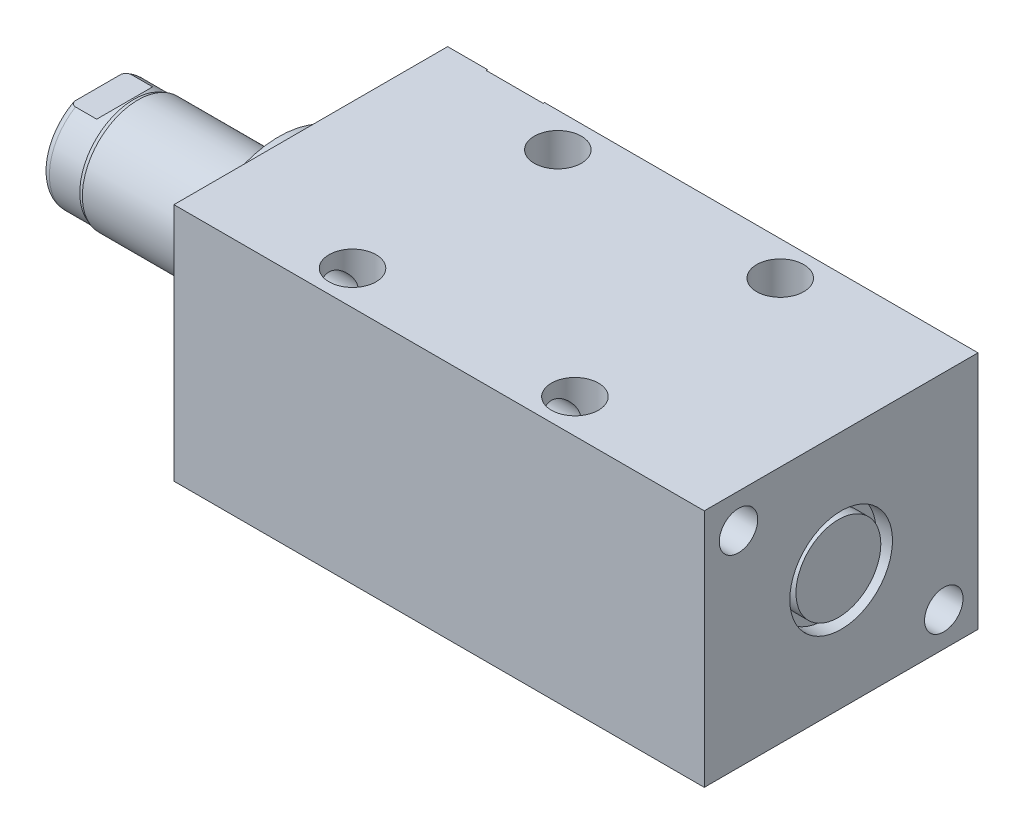
SolidWorks part; units mm, degrees
material "Alloy Steel"
ref_plane "Front Plane" through (0, 0, 0) normal (0, 0, 1) x (1, 0, 0)
ref_plane "Top Plane" through (0, 0, 0) normal (0, 1, 0) x (1, 0, 0)
ref_plane "Right Plane" through (0, 0, 0) normal (1, 0, 0) x (0, 0, -1)
ref_plane "Plane1" through (0, 0, 0) normal (1, 0, 0) x (0, 0, -1)
sketch "Sketch1" plane through (0, 0, 0) normal (1, 0, 0) x (0, 0, -1)
  line L0 (-25.4, 22.225) -> (25.4, 22.225)
  line L1 (25.4, 22.225) -> (25.4, -22.225)
  line L2 (25.4, -22.225) -> (-25.4, -22.225)
  line L3 (-25.4, -22.225) -> (-25.4, 22.225)
  line L4 (0, -24.4475) -> (0, 24.4475) construction
  dimension "D1" = 44.45
  dimension "D2" = 22.225
  dimension "D3" = 50.8
extrude "Extrude1" add sketch "Sketch1" along normal blind 98.425
ref_plane "Plane12" through (0, 14.3002, 0) normal (0, 1, 0) x (-1, 0, 0)
sketch "S2D0002" plane through (0, 14.3002, 0) normal (0, 1, 0) x (-1, 0, 0)
  line L0 (-18.8849, -25.146) -> (-22.225, -25.146)
  line L1 (-18.8849, -25.146) -> (-18.3423, -22.5933)
  line L2 (-18.3423, -22.5933) -> (-17.6784, -21.9294)
  line L3 (-17.6784, -21.9294) -> (-17.6784, -11.176)
  line L4 (-17.6784, -11.176) -> (-12.7, -11.176)
  line L5 (-12.7, -11.176) -> (-12.7, -25.4)
  line L6 (-12.7, -19.1384) -> (-12.7, 0.6985) construction
  line L7 (0, -25.4) -> (0, 25.4) construction
  line L8 (-22.225, -25.4) -> (-22.225, -25.146)
  line L9 (-98.425, -25.4) -> (0, -25.4) construction
  line L10 (-22.225, -25.4) -> (-12.7, -25.4)
  dimension "D1" = 14.224
  dimension "D2" = 12.7
  dimension "D3" = 9.9568
  dimension "D4" = 45
  dimension "D5" = 12.3698
  dimension "D6" = 12
  dimension "D7" = 2.5527
  dimension "D8" = 0.254
  dimension "D9" = 19.05
revolve "Cut-Revolve1" cut sketch "S2D0002" angle 360 about L6
ref_plane "Plane3" through (41.148, 0, -25.146) normal (0, 1, 0) x (1, 0, 0)
sketch "Sketch3" plane through (41.148, 0, -25.146) normal (0, 1, 0) x (1, 0, 0)
  line L0 (47.5869, 0) -> (50.927, 0)
  line L1 (47.5869, 0) -> (47.0443, -2.5527)
  line L2 (47.0443, -2.5527) -> (46.3804, -3.2166)
  line L3 (46.3804, -3.2166) -> (46.3804, -13.97)
  line L4 (46.3804, -13.97) -> (41.402, -13.97)
  line L5 (41.402, -13.97) -> (41.402, 0.254)
  line L6 (41.402, -21.9564) -> (41.402, 0.6985) construction
  line L7 (-41.148, 0.254) -> (-41.148, -50.546) construction
  line L8 (50.927, 0.254) -> (50.927, 0)
  line L9 (57.277, 0.254) -> (-23.1638, 0.254) construction
  line L10 (50.927, 0.254) -> (41.402, 0.254)
  dimension "D1" = 14.224
  dimension "D2" = 82.55
  dimension "D3" = 9.9568
  dimension "D4" = 45
  dimension "D5" = 12
  dimension "D6" = 12.3698
  dimension "D7" = 2.5527
  dimension "D8" = 0.254
  dimension "D9" = 19.05
revolve "Cut-Revolve2" cut sketch "Sketch3" angle 360 about L6
ref_plane "Plane4" through (53.975, 0, 0) normal (0, 0, 1) x (0, -1, 0)
sketch "Sketch4" plane through (53.975, 0, 0) normal (0, 0, 1) x (0, -1, 0)
  line L0 (6.1849, 41.402) -> (9.525, 41.402)
  line L1 (6.1849, 41.402) -> (5.6423, 38.8493)
  line L2 (5.6423, 38.8493) -> (4.9784, 38.1854)
  line L3 (4.9784, 38.1854) -> (4.9784, 30.0482)
  line L4 (4.9784, 30.0482) -> (0, 30.0482)
  line L5 (0, 30.0482) -> (0, 44.45)
  line L6 (0, -15.0954) -> (0, 0.5677) construction
  line L7 (0, 44.45) -> (9.525, 44.45)
  line L9 (-22.225, 44.45) -> (22.225, 44.45) construction
  line L10 (9.525, 44.45) -> (9.525, 41.402)
  dimension "D1" = 11.3538
  dimension "D2" = 9.9568
  dimension "D3" = 3.048
  dimension "D4" = 19.05
  dimension "D5" = 2.5527
  dimension "D6" = 12
  dimension "D7" = 45
  dimension "D8" = 12.3698
revolve "Cut-Revolve3" cut sketch "Sketch4" angle 360 about L6
sketch "Sketch5" plane through (0, 0, 0) normal (-1, 0, 0) x (0, 0, 1)
  circle A0 centre (0, 0) radius 17.4625
  dimension "D1" = 34.925
extrude "Extrude2" add sketch "Sketch5" along normal blind 5.969
ref_plane "Plane5" through (0, 0, 0) normal (0, -1, 0) x (0, 0, 1)
sketch "Sketch6" plane through (0, 0, 0) normal (0, -1, 0) x (0, 0, 1)
  line L0 (0, 5.969) -> (-10.3187, 5.969)
  line L1 (-10.3187, 5.969) -> (-10.3187, 39.497)
  line L2 (-10.3187, 39.497) -> (0, 39.497)
  line L3 (0, 39.497) -> (0, 5.969)
  line L4 (0, -5.7546) -> (0, 21.1709) construction
  line L5 (17.4625, 5.969) -> (-17.4625, 5.969) construction
  line L6 (25.4, -98.425) -> (-25.4, -98.425) construction
  dimension "D1" = 137.922
  dimension "D2" = 20.6375
revolve "Revolve1" add sketch "Sketch6" angle 360 about L4
ref_plane "Plane6" through (-18.5113, 3.2639, 0) normal (0, 0, 1) x (0, 1, 0)
sketch "S2D0001" plane through (-18.5113, 3.2639, 0) normal (0, 0, 1) x (0, 1, 0)
  line L0 (0, 19.05) -> (0, 5.9235)
  line L1 (0, 5.9235) -> (-3.2639, 5.9235)
  line L2 (1.1176, 20.9857) -> (-3.2639, 20.9857)
  line L3 (-3.2639, 20.9857) -> (-3.2639, 5.9235)
  line L4 (0, 19.05) -> (1.1176, 20.9857)
  line L5 (-3.2639, -18.5113) -> (-3.2639, 2.765) construction
  line L6 (7.0549, 20.9857) -> (-13.5826, 20.9857) construction
  dimension "D1" = 30
  dimension "D2" = 8.763
  dimension "D3" = 6.5278
  dimension "D4" = 15.0622
revolve "Cut-Revolve4" cut sketch "S2D0001" angle 360 about L5
ref_plane "Plane7" through (0, 0, 0) normal (0, 1, 0) x (0, 0, -1)
sketch "Sketch8" plane through (0, 0, 0) normal (0, 1, 0) x (0, 0, -1)
  line L0 (-10.3187, 32.0802) -> (-10.033, 32.8422)
  line L1 (-10.033, 32.8422) -> (-10.033, 38.481)
  line L2 (0, 12.6594) -> (0, 20.8178) construction
  line L3 (-10.3187, 32.0802) -> (-10.3187, 39.497)
  line L4 (-9.6449, 39.497) -> (-10.3187, 39.497)
  line L5 (10.3187, 39.497) -> (-10.3187, 39.497) construction
  line L6 (-10.3187, 39.497) -> (-10.3187, 5.969) construction
  arc A0 (-9.6449, 39.497) -> (-10.033, 38.481) centre (-8.509, 38.481) ccw
  dimension "D2" = 1.524
  dimension "D1" = 20.066
  dimension "D3" = 1.016
  dimension "D4" = 0.762
  dimension "D5" = 6.6548
revolve "Cut-Revolve5" cut sketch "Sketch8" angle 360 about L2
ref_plane "Plane11" through (0, 0, 0) normal (0, 0, -1) x (0, -1, 0)
sketch "Sketch12" plane through (0, 0, 0) normal (0, 0, -1) x (0, -1, 0)
  line L0 (8.5852, 39.497) -> (8.5852, 34.544)
  line L1 (8.5852, 34.544) -> (10.033, 33.0962)
  line L2 (-8.5852, 39.497) -> (-8.5852, 34.544)
  line L3 (-8.5852, 34.544) -> (-10.033, 33.0962)
  line L4 (8.5852, 39.497) -> (10.033, 39.497)
  line L5 (0, 13.7262) -> (0, 20.767) construction
  line L6 (-10.033, 33.0962) -> (-10.033, 39.497)
  line L7 (9.6449, 39.497) -> (-9.6449, 39.497) construction
  line L8 (10.033, 32.8422) -> (10.033, 38.481) construction
  line L9 (10.033, 33.0962) -> (10.033, 39.497)
  line L10 (-8.5852, 39.497) -> (-10.033, 39.497)
  dimension "D1" = 17.1704
  dimension "D2" = 4.953
  dimension "D3" = 45
extrude "Cut-Extrude4" cut sketch "Sketch12" against normal mid plane 60.96
sketch "Sketch13" plane through (0, 0, -25.146) normal (0, 0, -1) x (-1, 0, 0)
  circle A0 centre (-82.55, 0) radius 7.874
  circle A2 centre (-82.55, 0) radius 6.1849 construction
  dimension "D1" = 15.748
extrude "Extrude3" add sketch "Sketch13" along normal blind 2.54
hole_wizard "Hole1" positions "Sketch15" profile "Sketch14" legacy end condition up to next
sketch "Sketch15" plane through (0, 0, 0) normal (-1, 0, 0) x (0, 0, 1)
  line L0 (0, 0) -> (-29.9914, 0) construction
  line L1 (0, 0) -> (0, 25.7648) construction
  point P0 (-19.05, -15.875)
  point P11 (19.05, 15.875)
  dimension "D1" = 15.875
  dimension "D2" = 19.05
  dimension "D3" = 31.75
  dimension "D4" = 38.1
sketch "Sketch14" plane through (0, -15.875, -19.05) normal (0, 1, 0) x (0, 0, 1)
  line L0 (0, 0) -> (0, 98.425)
  line L1 (0, 98.425) -> (3.5687, 98.425)
  line L2 (3.5687, 98.425) -> (3.5687, 0)
  line L3 (3.5687, 0) -> (0, 0)
  line L4 (0, 110) -> (0, -10) construction
  dimension "Diameter" = 7.1374
  dimension "Depth" = 98.425
hole_wizard "Hole2" positions "Sketch17" profile "Sketch16" legacy
sketch "Sketch17" plane through (0, 22.225, 0) normal (0, 1, 0) x (-1, 0, 0)
  line L0 (0, 0) -> (-59.3363, 0) construction
  line L1 (0, -25.4) -> (0, 25.4) construction
  point P0 (-26.797, -19.05)
  point P9 (-26.797, 19.05)
  dimension "D1" = 38.1
  dimension "D2" = 26.797
sketch "Sketch16" plane through (26.797, 22.225, -19.05) normal (1, 0, 0) x (0, 0, 1)
  line L0 (0, 0) -> (0, 44.45)
  line L1 (0, 44.45) -> (4.3688, 44.45)
  line L2 (4.3688, 44.45) -> (4.3688, 0)
  line L3 (4.3688, 0) -> (0, 0)
  line L4 (0, 110) -> (0, -10) construction
  dimension "Diameter" = 8.7376
  dimension "Depth" = 44.45
pattern_linear "LPattern1" count 2 spacing 41.275 along (1, 0, 0) of "Hole2"
sketch "Sketch18" plane through (95.377, 0, 0) normal (1, 0, 0) x (0, 0, -1)
  circle A0 centre (0, 0) radius 7.874
  dimension "D1" = 15.748
extrude "Extrude4" add sketch "Sketch18" along normal blind 2.54
